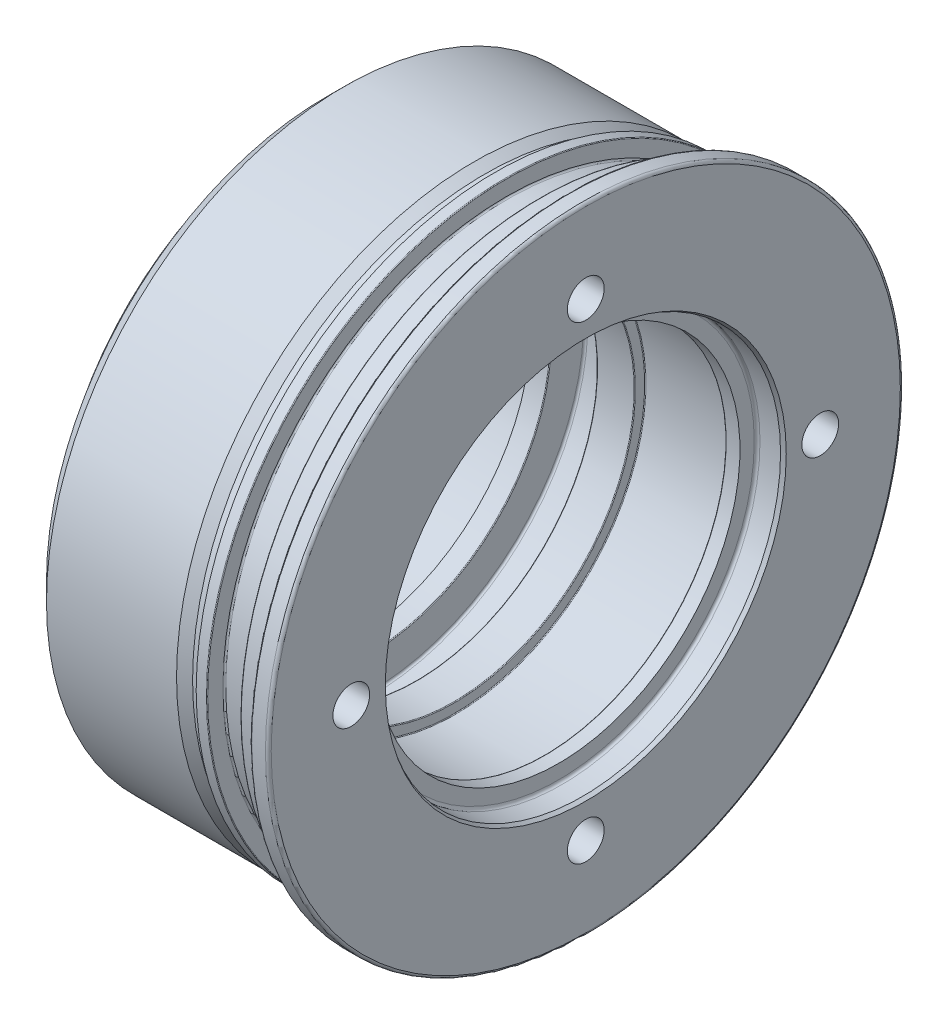
SolidWorks part; units mm, degrees
ref_plane "Front" through (0, 0, 0) normal (0, 0, 1) x (1, 0, 0)
ref_plane "Top" through (0, 0, 0) normal (0, 1, 0) x (1, 0, 0)
ref_plane "Right" through (0, 0, 0) normal (1, 0, 0) x (0, 0, -1)
sketch "Sketch1" plane through (0, 0, 0) normal (0, 0, 1) x (1, 0, 0)
  line L0 (-77.5, 0) -> (0, 0) construction
  line L1 (0, 55.5774) -> (0, 87.2)
  line L2 (-0.8, 88) -> (-4.6, 88)
  line L3 (-12.5, 83) -> (-5.8, 83)
  line L4 (-12.7, 82.8) -> (-12.7, 78.6)
  line L5 (-13.1, 78.2) -> (-21.6, 78.2)
  line L6 (-22, 78.6) -> (-22, 82.8)
  line L7 (-22.2, 83) -> (-25, 83)
  line L8 (-25, 83) -> (-25, 81)
  line L9 (-25, 81) -> (-28, 81)
  line L10 (-28, 81) -> (-30.9439, 82.5)
  line L11 (-30.9439, 82.5) -> (-67, 82.5)
  line L12 (-77.5, 70) -> (-72, 70)
  line L13 (-77.5, 70) -> (-77.5, 52)
  line L14 (-77.5, 52) -> (-65.5, 52)
  line L15 (-65.5, 52) -> (-65.5, 50.25)
  line L16 (-65.5, 50.25) -> (-60.2, 50.25)
  line L17 (-60, 50.45) -> (-60, 59.4)
  line L18 (-59.4, 60) -> (-47.6, 60)
  line L19 (-47, 59.4) -> (-47, 50.3)
  line L20 (-46.8, 50.1) -> (-36.7, 50.1)
  line L21 (-36.5, 50.3) -> (-36.5, 52.8)
  line L22 (-36.3, 53) -> (-11.7, 53)
  line L23 (-11.5, 52.8) -> (-11.5, 50.45)
  line L24 (-11.3, 50.25) -> (-7.5, 50.25)
  line L25 (-7.5, 50.25) -> (-7.5, 54.2)
  line L26 (-6.7, 55) -> (-1, 55)
  line L27 (-1, 55) -> (0, 55.5774)
  line L28 (-72, 70) -> (-72, 77.5)
  line L29 (-72, 77.5) -> (-67, 82.5)
  line L30 (-5, 83.8) -> (-5, 87.6)
  arc A0 (0, 87.2) -> (-0.8, 88) centre (-0.8, 87.2) ccw
  arc A1 (-4.6, 88) -> (-5, 87.6) centre (-4.6, 87.6) ccw
  arc A2 (-5.8, 83) -> (-5, 83.8) centre (-5.8, 83.8) ccw
  arc A3 (-12.7, 78.6) -> (-13.1, 78.2) centre (-13.1, 78.6) cw
  arc A4 (-21.6, 78.2) -> (-22, 78.6) centre (-21.6, 78.6) cw
  arc A5 (-12.5, 83) -> (-12.7, 82.8) centre (-12.5, 82.8) ccw
  arc A6 (-22, 82.8) -> (-22.2, 83) centre (-22.2, 82.8) ccw
  arc A7 (-11.7, 53) -> (-11.5, 52.8) centre (-11.7, 52.8) cw
  arc A8 (-36.5, 52.8) -> (-36.3, 53) centre (-36.3, 52.8) cw
  arc A9 (-47.6, 60) -> (-47, 59.4) centre (-47.6, 59.4) cw
  arc A10 (-60, 59.4) -> (-59.4, 60) centre (-59.4, 59.4) cw
  arc A11 (-7.5, 54.2) -> (-6.7, 55) centre (-6.7, 54.2) cw
  arc A12 (-60.2, 50.25) -> (-60, 50.45) centre (-60.2, 50.45) ccw
  arc A13 (-47, 50.3) -> (-46.8, 50.1) centre (-46.8, 50.3) ccw
  arc A14 (-36.7, 50.1) -> (-36.5, 50.3) centre (-36.7, 50.3) ccw
  arc A15 (-11.5, 50.45) -> (-11.3, 50.25) centre (-11.3, 50.45) ccw
  point P35 (0, 88)
  point P54 (-47, 60)
  point P57 (-60, 60)
  dimension "D33" = 0.8
  dimension "D34" = 0.4
  dimension "D35" = 0.4
  dimension "D36" = 0.2
  dimension "D37" = 0.2
  dimension "D38" = 0.6
  dimension "D39" = 0.8
  dimension "D40" = 0.2
  dimension "D43" = 0.8
  dimension "D2" = 110
  dimension "D3" = 100.5
  dimension "D4" = 106
  dimension "D5" = 13
  dimension "D6" = 120
  dimension "D7" = 104
  dimension "D8" = 77.5
  dimension "D9" = 1
  dimension "D10" = 7.5
  dimension "D11" = 140
  dimension "D12" = 3
  dimension "D13" = 27
  dimension "D14" = 9.3
  dimension "D15" = 3
  dimension "D16" = 52.5
  dimension "D17" = 5.5
  dimension "D18" = 72.5
  dimension "D19" = 166
  dimension "D20" = 176
  dimension "D21" = 30
  dimension "D22" = 165
  dimension "D23" = 12
  dimension "D24" = 17.5
  dimension "D25" = 41
  dimension "D26" = 25
  dimension "D27" = 156.4
  dimension "D28" = 162
  dimension "D29" = 10.5
  dimension "D30" = 45
  dimension "D31" = 155
  dimension "D32" = 4.8
  dimension "D41" = 100.2
  dimension "D42" = 100.5
revolve "Base-Revolve" add sketch "Sketch1" angle 360 about L0
cosmetic thread "Cosmetic Thread1" parameters "D2"=162.835
hole_wizard "4 stk ø10.2 x 12 huller" positions "Sketch3" profile "Sketch2" legacy
sketch "Sketch3" plane through (0, 0, 0) normal (1, 0, 0) x (0, 0, -1)
  line L0 (0, 0) -> (0, 65) construction
  line L2 (0, 0) -> (65, 0) construction
  circle A0 centre (0, 0) radius 65 construction
  point P0 (0, 65)
  point P17 (65, 0)
  point P19 (0, -65)
  point P22 (-65, 0)
  dimension "D1" = 130
sketch "Sketch2" plane through (0, 65, 0) normal (0, 1, 0) x (0, 0, -1)
  line L0 (0, 0) -> (0, 15.0644)
  line L1 (0, 15.0644) -> (5.1, 12)
  line L2 (5.1, 12) -> (5.1, 0)
  line L4 (5.1, 0) -> (0, 0)
  line L6 (0, 15.0644) -> (-5.1, 12) construction
  line L7 (0, -4.2442) -> (0, 117.3081) construction
  dimension "Diameter" = 10.2
  dimension "Depth" = 12
  dimension "Drill Angle" = 118
